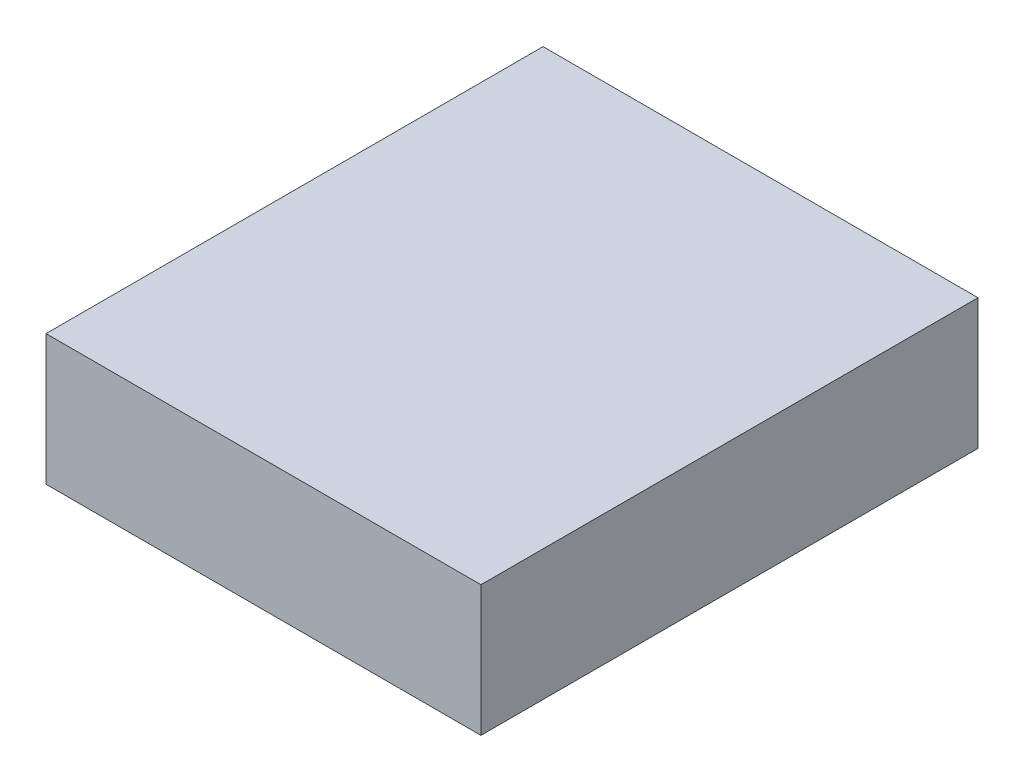
SolidWorks part; units mm, degrees
ref_plane "Front Plane" through (0, 0, 0) normal (0, 0, 1) x (1, 0, 0)
ref_plane "Top Plane" through (0, 0, 0) normal (0, 1, 0) x (1, 0, 0)
ref_plane "Right Plane" through (0, 0, 0) normal (1, 0, 0) x (0, 0, -1)
sketch "Sketch1" plane through (0, 0, 0) normal (0, 1, 0) x (1, 0, 0)
  line L1 (1.75, 2) -> (-1.75, 2)
  line L2 (1.75, 2) -> (1.75, -2)
  line L3 (1.75, -2) -> (-1.75, -2)
  line L4 (-1.75, 2) -> (-1.75, -2)
  line L5 (1.75, 2) -> (-1.75, -2) construction
  line L6 (1.75, -2) -> (-1.75, 2) construction
  point P0 (0, 0)
  dimension "D1" = 4
  dimension "D2" = 3.5
extrude "Boss-Extrude1" add sketch "Sketch1" along normal blind 1.05
